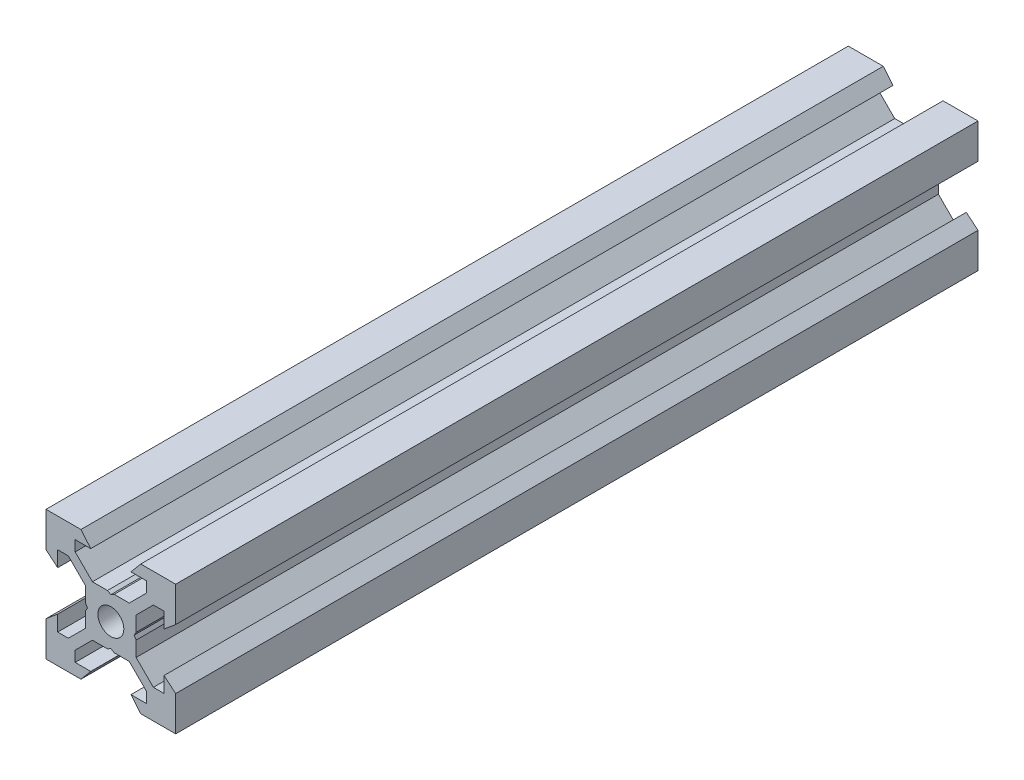
SolidWorks part; units mm, degrees
ref_plane "Front Plane" through (0, 0, 0) normal (0, 0, 1) x (1, 0, 0)
ref_plane "Top Plane" through (0, 0, 0) normal (0, 1, 0) x (1, 0, 0)
ref_plane "Right Plane" through (0, 0, 0) normal (1, 0, 0) x (0, 0, -1)
sketch "Sketch1" plane through (0, 0, 0) normal (0, 0, 1) x (1, 0, 0)
  line L0 (10, 10) -> (4.6104, 10) construction
  line L1 (10, 10) -> (10, 4.6104) construction
  line L2 (10, -10) -> (10, -4.6104) construction
  line L3 (10, -10) -> (4.6104, -10) construction
  line L4 (10, 10) -> (10, 4.6104)
  line L5 (6.5607, 5.5) -> (8.2, 5.5)
  line L6 (5.5, 8.2) -> (5.5, 6.5607)
  line L7 (10, 10) -> (4.6104, 10)
  line L8 (10, 10) -> (10, 4.6104)
  line L9 (6.5607, 5.5) -> (3.9, 2.8393)
  line L10 (5.5, 6.5607) -> (2.8393, 3.9)
  line L11 (10, 4.6104) -> (8.2, 3.1)
  line L12 (4.6104, 10) -> (3.1, 8.2)
  line L13 (8.2, 3.1) -> (8.2, 5.5)
  line L14 (3.1, 8.2) -> (5.5, 8.2)
  line L15 (-6.5607, 5.5) -> (-8.2, 5.5)
  line L16 (6.5607, -5.5) -> (8.2, -5.5)
  line L17 (3.1, -8.2) -> (5.5, -8.2)
  line L18 (8.2, -3.1) -> (8.2, -5.5)
  line L19 (4.6104, -10) -> (3.1, -8.2)
  line L20 (10, -4.6104) -> (8.2, -3.1)
  line L21 (0.5196, -3.9) -> (0, -3.6)
  line L22 (0.5196, 3.9) -> (0, 3.6)
  line L23 (3.6, 0) -> (3.9, -0.5196)
  line L24 (3.9, 0.5196) -> (3.6, 0)
  line L25 (3.9, 0.5196) -> (3.9, 2.8393)
  line L26 (2.8393, 3.9) -> (0.5196, 3.9)
  line L27 (3.9, -2.8393) -> (3.9, -0.5196)
  line L28 (2.8393, -3.9) -> (0.5196, -3.9)
  line L29 (5.5, -6.5607) -> (2.8393, -3.9)
  line L30 (6.5607, -5.5) -> (3.9, -2.8393)
  line L31 (10, -10) -> (10, -4.6104)
  line L32 (10, -10) -> (4.6104, -10)
  line L33 (5.5, -8.2) -> (5.5, -6.5607)
  line L34 (-6.5607, -5.5) -> (-8.2, -5.5)
  line L35 (10, -10) -> (10, -4.6104)
  line L36 (0, 0) -> (0, 8.2) construction
  line L37 (-10, -10) -> (-4.6104, -10) construction
  line L38 (-10, -10) -> (-10, -4.6104) construction
  line L39 (-10, 10) -> (-10, 4.6104) construction
  line L40 (-10, 10) -> (-4.6104, 10) construction
  line L41 (-10, -10) -> (-10, -4.6104)
  line L43 (-5.5, -8.2) -> (-5.5, -6.5607)
  line L44 (-10, -10) -> (-4.6104, -10)
  line L45 (-10, -10) -> (-10, -4.6104)
  line L46 (-6.5607, -5.5) -> (-3.9, -2.8393)
  line L47 (-5.5, -6.5607) -> (-2.8393, -3.9)
  line L48 (-2.8393, -3.9) -> (-0.5196, -3.9)
  line L49 (-3.9, -2.8393) -> (-3.9, -0.5196)
  line L50 (-2.8393, 3.9) -> (-0.5196, 3.9)
  line L51 (-3.9, 0.5196) -> (-3.9, 2.8393)
  line L52 (-3.9, 0.5196) -> (-3.6, 0)
  line L53 (-3.6, 0) -> (-3.9, -0.5196)
  line L54 (-0.5196, 3.9) -> (0, 3.6)
  line L55 (-0.5196, -3.9) -> (0, -3.6)
  line L56 (-10, -4.6104) -> (-8.2, -3.1)
  line L57 (-4.6104, -10) -> (-3.1, -8.2)
  line L58 (-8.2, -3.1) -> (-8.2, -5.5)
  line L59 (-3.1, -8.2) -> (-5.5, -8.2)
  line L60 (-10, -10) -> (10, -10) construction
  line L61 (-10, -10) -> (-10, 10) construction
  line L62 (-3.1, 8.2) -> (-5.5, 8.2)
  line L63 (-8.2, 3.1) -> (-8.2, 5.5)
  line L64 (-4.6104, 10) -> (-3.1, 8.2)
  line L65 (-10, 4.6104) -> (-8.2, 3.1)
  line L66 (-5.5, 6.5607) -> (-2.8393, 3.9)
  line L67 (-6.5607, 5.5) -> (-3.9, 2.8393)
  line L68 (-10, 10) -> (-10, 4.6104)
  line L69 (-10, 10) -> (-4.6104, 10)
  line L70 (-5.5, 8.2) -> (-5.5, 6.5607)
  line L71 (-10, 10) -> (10, 10) construction
  line L72 (-10, 10) -> (-10, 4.6104)
  line L73 (10, -10) -> (10, 10) construction
  line L74 (-10, -10) -> (10, 10) construction
  line L75 (-10, 10) -> (10, -10) construction
  circle A0 centre (0, 0) radius 2
  dimension "D7" = 4
  dimension "D1" = 20
  dimension "D2" = 5.3896
  dimension "D3" = 4.5
  dimension "D4" = 50
  dimension "D5" = 1.8
  dimension "D6" = 1.5104
  dimension "D8" = 5.5
  dimension "D9" = 120
  dimension "D10" = 0.3
  dimension "D11" = 2.3197
  dimension "D12" = 7.8
  dimension "D13" = 7.8
  dimension "D14" = 1.5
  dimension "D15" = 2.6607
extrude "Boss-Extrude1" add sketch "Sketch1" along normal mid plane 123.74 contours L70 L62 L64 L69 L68 L65 L63 L15 L67 L51 L52 L53 L49 L46 L34 L58 L56 L41 L44 L57 L59 L43 L47 L48 L55 L21 L28 L29 L33 L17 L19 L32 L31 L20 L18 L16 L30 L27 L23 L24 L25 L9 L5 L13 L11 L4 L7 L12 L14 L6 L10
